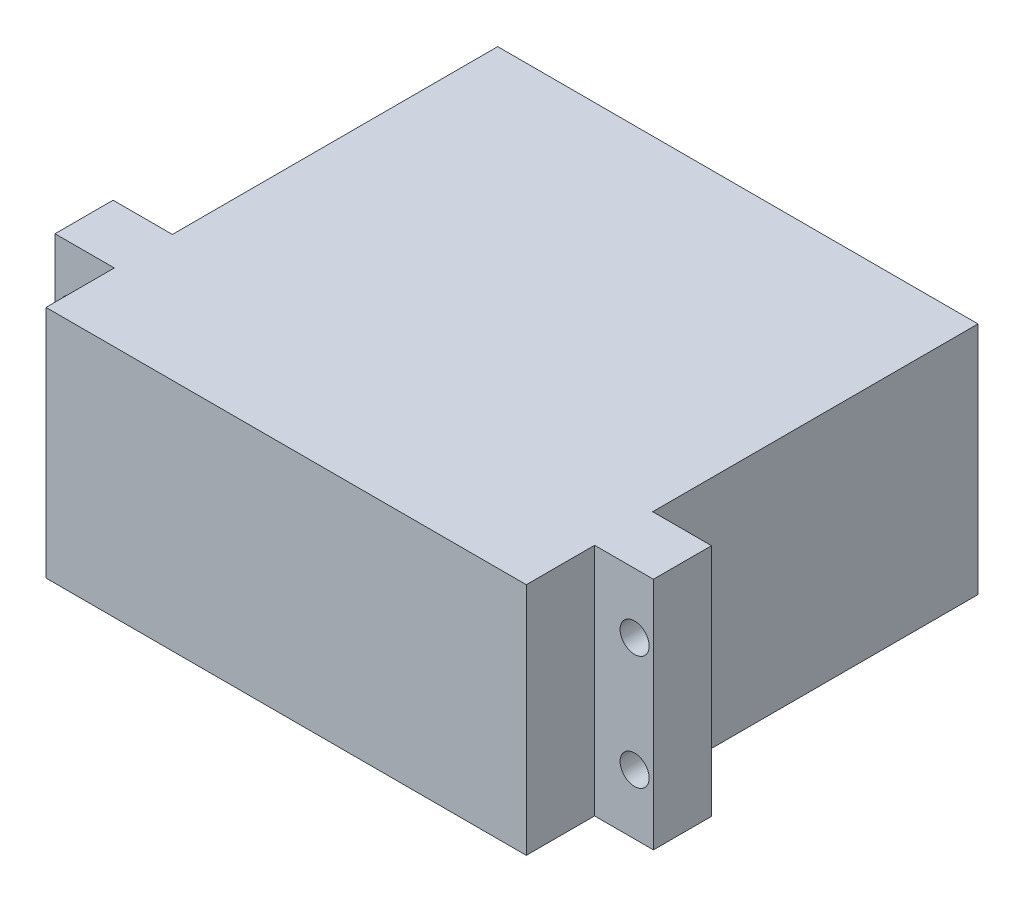
SolidWorks part; units mm, degrees
ref_plane "Front Plane" through (0, 0, 0) normal (0, 0, 1) x (1, 0, 0)
ref_plane "Top Plane" through (0, 0, 0) normal (0, 1, 0) x (1, 0, 0)
ref_plane "Right Plane" through (0, 0, 0) normal (1, 0, 0) x (0, 0, -1)
sketch "Sketch1" plane through (0, 0, 0) normal (0, 0, 1) x (1, 0, 0)
  line L1 (0, 0) -> (42, 0)
  line L2 (0, 0) -> (0, 20.5)
  line L3 (0, 20.5) -> (42, 20.5)
  line L4 (42, 0) -> (42, 20.5)
  dimension "D1" = 20.5
  dimension "D2" = 42
extrude "Boss-Extrude1" add sketch "Sketch1" along normal blind 39.5
ref_plane "Plane1" through (0, 0, 28.448) normal (0, 0, -1) x (-1, 0, 0)
sketch "Sketch2" plane through (0, 0, 28.448) normal (0, 0, -1) x (-1, 0, 0)
  line L0 (0, 0) -> (-42, 0) construction
  line L1 (-21, 20.5) -> (-21, 0) construction
  line L2 (0, 10.25) -> (-42, 10.25) construction
  line L3 (5.1851, 20.5) -> (-47.1446, 20.5)
  line L4 (5.1851, 20.5) -> (5.1851, 0)
  line L5 (-42, 20.5) -> (0, 20.5) construction
  line L6 (-42, 0) -> (-42, 20.5) construction
  line L7 (0, 20.5) -> (0, 0) construction
  line L8 (0, 0) -> (-42, 0)
  line L9 (-42, 20.5) -> (0, 20.5)
  line L10 (-42, 0) -> (-42, 20.5)
  line L11 (0, 20.5) -> (0, 0)
  line L12 (5.1851, 0) -> (-47.1446, 0)
  line L13 (-47.1446, 20.5) -> (-47.1446, 0)
  line L18 (-42, 20.5) -> (0, 20.5) construction
  line L19 (0, 0) -> (-42, 0) construction
  circle A0 centre (-45.5, 15.25) radius 1.27
  circle A1 centre (-45.5, 5.25) radius 1.27
  circle A2 centre (3.5, 15.25) radius 1.27
  circle A3 centre (3.5, 5.25) radius 1.27
  dimension "D5" = 2.54
  dimension "D1" = 49
  dimension "D2" = 10
  dimension "D3" = 49
  dimension "D4" = 10
extrude "Boss-Extrude2" add sketch "Sketch2" against normal blind 5.08
